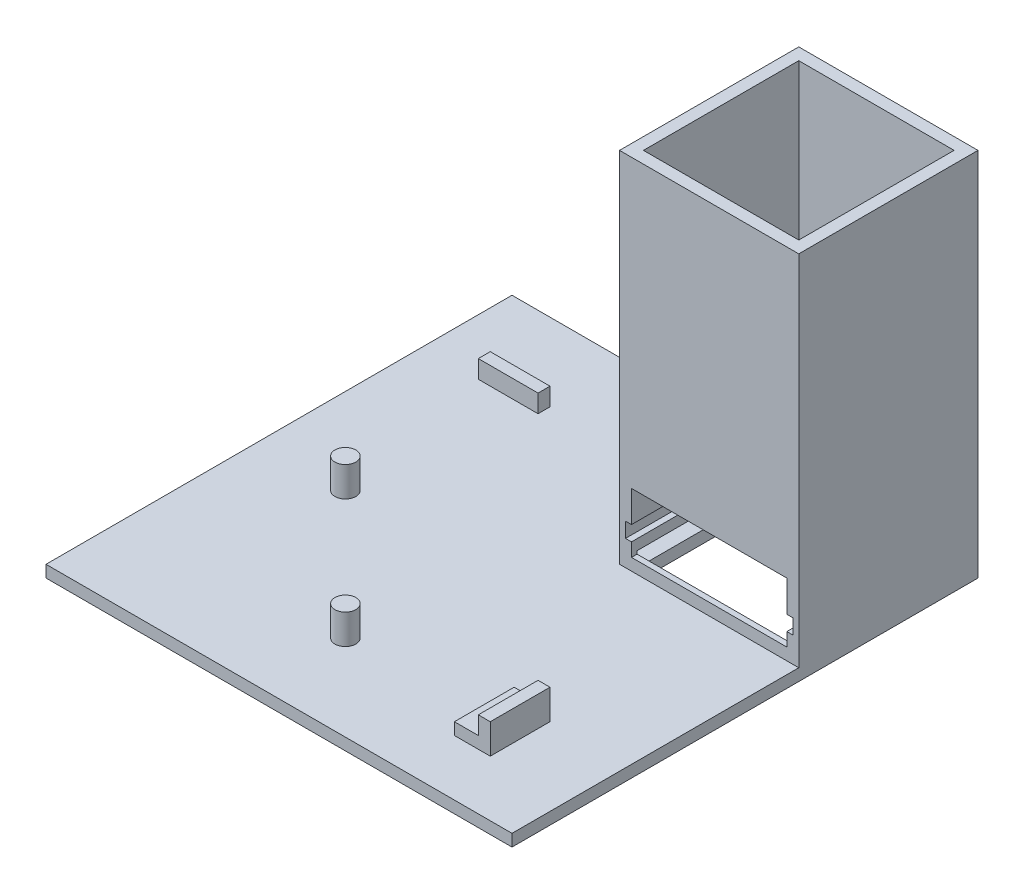
SolidWorks part; units mm, degrees
ref_plane "Front Plane" through (0, 0, 0) normal (0, 0, 1) x (1, 0, 0)
ref_plane "Top Plane" through (0, 0, 0) normal (0, 1, 0) x (1, 0, 0)
ref_plane "Right Plane" through (0, 0, 0) normal (1, 0, 0) x (0, 0, -1)
sketch "Sketch1" plane through (0, 0, 0) normal (0, 1, 0) x (1, 0, 0)
  line L1 (-39, -39) -> (39, -39)
  line L2 (-39, -39) -> (-39, 39)
  line L3 (-39, 39) -> (39, 39)
  line L4 (39, -39) -> (39, 39)
  line L5 (-39, -39) -> (39, 39) construction
  line L6 (-39, 39) -> (39, -39) construction
  point P0 (0, 0)
  dimension "D1" = 78
  dimension "D2" = 78
extrude "Boss-Extrude1" add sketch "Sketch1" along normal blind 2
sketch "Sketch2" plane through (0, 2, 0) normal (0, 1, 0) x (1, 0, 0)
  line L1 (39, 39) -> (9, 39)
  line L2 (39, 39) -> (39, 9)
  line L3 (39, 9) -> (9, 9)
  line L4 (9, 39) -> (9, 9)
  dimension "D1" = 30
  dimension "D2" = 30
extrude "Boss-Extrude2" add sketch "Sketch2" along normal blind 60
sketch "Sketch3" plane through (0, 62, 0) normal (0, 1, 0) x (1, 0, 0)
  line L2 (11, 11) -> (37, 11)
  line L3 (11, 11) -> (11, 37)
  line L4 (11, 37) -> (37, 37)
  line L5 (37, 11) -> (37, 37)
  line L6 (11, 11) -> (37, 37) construction
  line L7 (11, 37) -> (37, 11) construction
  point P4 (24, 24)
  dimension "D1" = 26
extrude "Cut-Extrude1" cut sketch "Sketch3" against normal blind 62
sketch "Sketch4" plane through (9, 0, 0) normal (-1, 0, 0) x (0, 0, 1)
  line L3 (-37.9345, 2) -> (-9.9345, 2)
  line L4 (-37.9345, 2) -> (-37.9345, 4.5)
  line L5 (-37.9345, 4.5) -> (-9.9345, 4.5)
  line L6 (-9.9345, 2) -> (-9.9345, 4.5)
  line L7 (-37.9345, 2) -> (-9.9345, 4.5) construction
  line L8 (-37.9345, 4.5) -> (-9.9345, 2) construction
  point P4 (-23.9345, 3.25)
  dimension "D2" = 28
extrude "Cut-Extrude2" cut sketch "Sketch4" against normal blind 28
sketch "Sketch5" plane through (0, 0, -9) normal (0, 0, 1) x (1, 0, 0)
  line L1 (37, 2) -> (37, 4.5) construction
  line L2 (11, 4.5) -> (11, 62) construction
  line L3 (37, 4) -> (11, 4)
  line L4 (37, 4) -> (37, 14)
  line L5 (37, 14) -> (11, 14)
  line L6 (11, 4) -> (11, 14)
  dimension "D2" = 10
extrude "Cut-Extrude3" cut sketch "Sketch5" against normal blind 2
sketch "Sketch6" plane through (37, 0, 0) normal (-1, 0, 0) x (0, 0, 1)
  line L1 (-9, 4) -> (-9, 14) construction
  line L3 (-37, 4.5) -> (-37, 62) construction
  line L4 (-9, 6.25) -> (-37, 6.25)
  line L5 (-9, 6.25) -> (-9, 8.75)
  line L6 (-9, 8.75) -> (-37, 8.75)
  line L7 (-37, 6.25) -> (-37, 8.75)
  dimension "D2" = 2.5
extrude "Cut-Extrude4" cut sketch "Sketch6" against normal blind 1
sketch "Sketch7" plane through (11, 0, 0) normal (1, 0, 0) x (0, 0, -1)
  line L1 (37, 8.75) -> (9, 8.75)
  line L2 (37, 8.75) -> (37, 6.25)
  line L3 (37, 6.25) -> (9, 6.25)
  line L4 (9, 8.75) -> (9, 6.25)
extrude "Cut-Extrude5" cut sketch "Sketch7" against normal blind 1
sketch "Sketch14" plane through (0, 2, 0) normal (0, 1, 0) x (1, 0, 0)
  line L0 (9, 9) -> (39, 9)
  line L1 (24, 9) -> (24, -24.64)
  line L2 (24, -24.64) -> (-3.25, -24.64)
  circle A0 centre (-3.25, -24.64) radius 1.75
  dimension "D3" = 3.5
  dimension "D1" = 33.64
  dimension "D2" = 27.25
extrude "Boss-Extrude8" add sketch "Sketch14" along normal blind 5 contours A0
sketch "Sketch15" plane through (0, 2, 0) normal (0, 1, 0) x (1, 0, 0)
  line L0 (9, 39) -> (9, 9)
  line L1 (9, 24) -> (-24.64, 24)
  line L2 (-24.64, 24) -> (-24.64, -3.25)
  circle A0 centre (-24.64, -3.25) radius 1.75
  dimension "D3" = 3.5
  dimension "D1" = 33.64
  dimension "D2" = 27.25
extrude "Boss-Extrude9" add sketch "Sketch15" along normal blind 5 contours A0
sketch "Sketch16" plane through (0, 2, 0) normal (0, 1, 0) x (1, 0, 0)
  line L0 (24, 9) -> (24, -24.64)
  line L1 (9, 9) -> (39, 9) construction
  line L3 (24, -24.64) -> (20, -24.64)
  line L4 (24, -24.64) -> (24, -19.64)
  line L5 (24, -19.64) -> (20, -19.64)
  line L6 (20, -24.64) -> (20, -19.64)
  line L7 (24, -24.64) -> (20, -24.64)
  line L8 (24, -24.64) -> (24, -29.64)
  line L9 (24, -29.64) -> (20, -29.64)
  line L10 (20, -24.64) -> (20, -29.64)
  dimension "D1" = 33.64
  dimension "D2" = 5
  dimension "D3" = 4
  dimension "D4" = 5
extrude "Boss-Extrude10" add sketch "Sketch16" along normal blind 2 contours L6 L3 L0 L5 | L3 L10 L9 L8
sketch "Sketch17" plane through (0, 2, 0) normal (0, 1, 0) x (1, 0, 0)
  line L1 (24, -19.64) -> (26, -19.64)
  line L2 (24, -19.64) -> (24, -29.64)
  line L3 (24, -29.64) -> (26, -29.64)
  line L4 (26, -19.64) -> (26, -29.64)
  dimension "D1" = 10
  dimension "D2" = 2
extrude "Boss-Extrude11" add sketch "Sketch17" along normal blind 5
sketch "Sketch18" plane through (0, 2, 0) normal (0, 1, 0) x (1, 0, 0)
  line L0 (9, 24) -> (-19.64, 24)
  line L1 (9, 39) -> (9, 9) construction
  line L3 (-19.64, 24) -> (-29.64, 24)
  line L4 (-19.64, 24) -> (-19.64, 26)
  line L5 (-19.64, 26) -> (-29.64, 26)
  line L6 (-29.64, 24) -> (-29.64, 26)
  dimension "D1" = 28.64
  dimension "D2" = 2
  dimension "D3" = 10
extrude "Boss-Extrude12" add sketch "Sketch18" along normal blind 3 contours L6 L3 L4 L5
